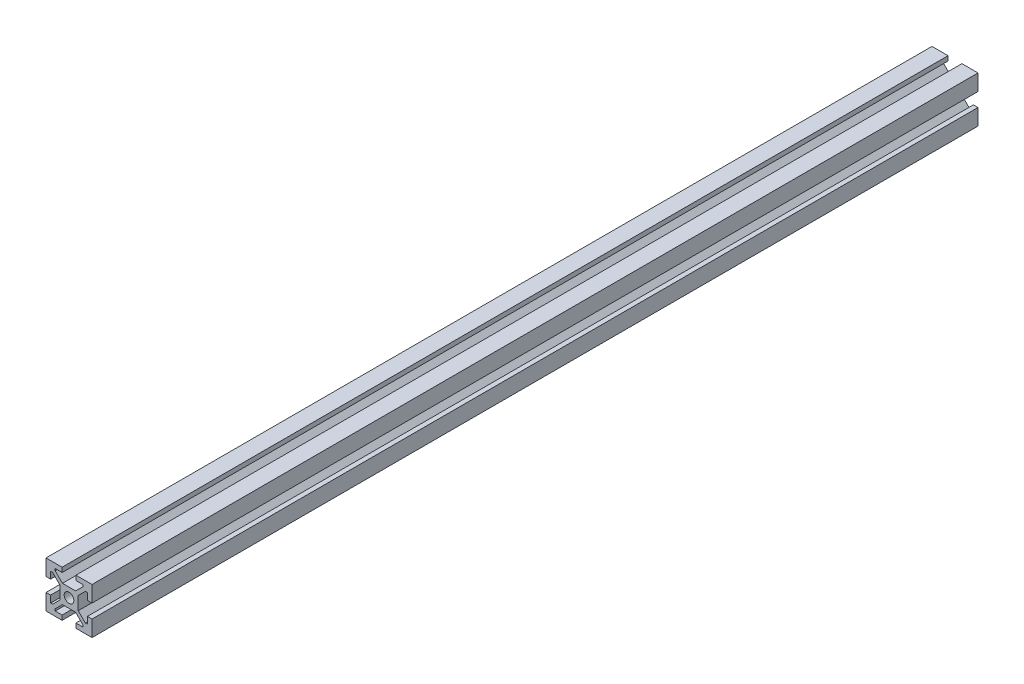
SolidWorks part; units mm, degrees
ref_plane "Alzado" through (0, 0, 0) normal (0, 0, 1) x (1, 0, 0)
ref_plane "Planta" through (0, 0, 0) normal (0, 1, 0) x (1, 0, 0)
ref_plane "Vista lateral" through (0, 0, 0) normal (1, 0, 0) x (0, 0, -1)
sketch "Croquis1" plane through (0, 0, 0) normal (0, 0, 1) x (1, 0, 0)
  line L0 (-3, 10) -> (-3, 8)
  line L1 (10, -10) -> (3, -10)
  line L2 (10, -10) -> (10, -3)
  line L3 (10, 10) -> (3, 10)
  line L4 (-10, -10) -> (-10, -3)
  line L5 (10, -10) -> (-10, 10) construction
  line L6 (10, 10) -> (-10, -10) construction
  line L7 (-3, 8) -> (-6, 8)
  line L8 (-6, 8) -> (-6, 7.13)
  line L9 (-6, 7.13) -> (-2.87, 4)
  line L10 (-2.87, 4) -> (2.87, 4)
  line L11 (2.87, 4) -> (6, 7.13)
  line L12 (6, 7.13) -> (6, 8)
  line L13 (6, 8) -> (3, 8)
  line L14 (3, 8) -> (3, 10)
  line L15 (-10, 3) -> (-8, 3)
  line L16 (-8, 3) -> (-8, 6)
  line L17 (-8, 6) -> (-7.13, 6)
  line L18 (-7.13, 6) -> (-4, 2.87)
  line L19 (-4, 2.87) -> (-4, -2.87)
  line L20 (-12.77, 0) -> (13.5697, 0) construction
  line L21 (10, 3) -> (8, 3)
  line L22 (8, 3) -> (8, 6)
  line L23 (8, 6) -> (7.13, 6)
  line L24 (7.13, 6) -> (4, 2.87)
  line L25 (4, 2.87) -> (4, -2.87)
  line L26 (-3, 10) -> (-10, 10)
  line L27 (10, 3) -> (10, 10)
  line L28 (-10, 3) -> (-10, 10)
  line L29 (-7.13, -6) -> (-4, -2.87)
  line L30 (-8, -6) -> (-7.13, -6)
  line L31 (-8, -3) -> (-8, -6)
  line L32 (-10, -3) -> (-8, -3)
  line L34 (-3, -10) -> (-10, -10)
  line L35 (-3, -10) -> (-3, -8)
  line L36 (-3, -8) -> (-6, -8)
  line L37 (-6, -8) -> (-6, -7.13)
  line L38 (-6, -7.13) -> (-2.87, -4)
  line L39 (-2.87, -4) -> (2.87, -4)
  line L40 (2.87, -4) -> (6, -7.13)
  line L41 (6, -7.13) -> (6, -8)
  line L42 (6, -8) -> (3, -8)
  line L43 (3, -8) -> (3, -10)
  line L46 (10, -3) -> (8, -3)
  line L47 (8, -3) -> (8, -6)
  line L48 (8, -6) -> (7.13, -6)
  line L49 (7.13, -6) -> (4, -2.87)
  circle A0 centre (0, 0) radius 2.1
  point P0 (0, 0)
  point P33 (-4, 0)
  point P52 (4, 0)
  dimension "D24" = 4.2
  dimension "D1" = 20
  dimension "D2" = 0.87
  dimension "D3" = 3
  dimension "D4" = 2
  dimension "D5" = 7
  dimension "D6" = 6
  dimension "D7" = 135
  dimension "D8" = 5.74
  dimension "D9" = 3
  dimension "D10" = 6
  dimension "D11" = 2
  dimension "D12" = 2
  dimension "D13" = 3
  dimension "D14" = 0.87
  dimension "D15" = 6
  dimension "D16" = 135
  dimension "D17" = 7
  dimension "D18" = 2
  dimension "D19" = 3
  dimension "D20" = 6
  dimension "D21" = 135
  dimension "D22" = 7
  dimension "D23" = 0.87
extrude "Saliente-Extruir2" add sketch "Croquis1" against normal blind 385
cosmetic thread "Rosca cosmética1" parameters "D1"=12, "D2"=5
cosmetic thread "Rosca cosmética2" parameters "D1"=12, "D2"=5
